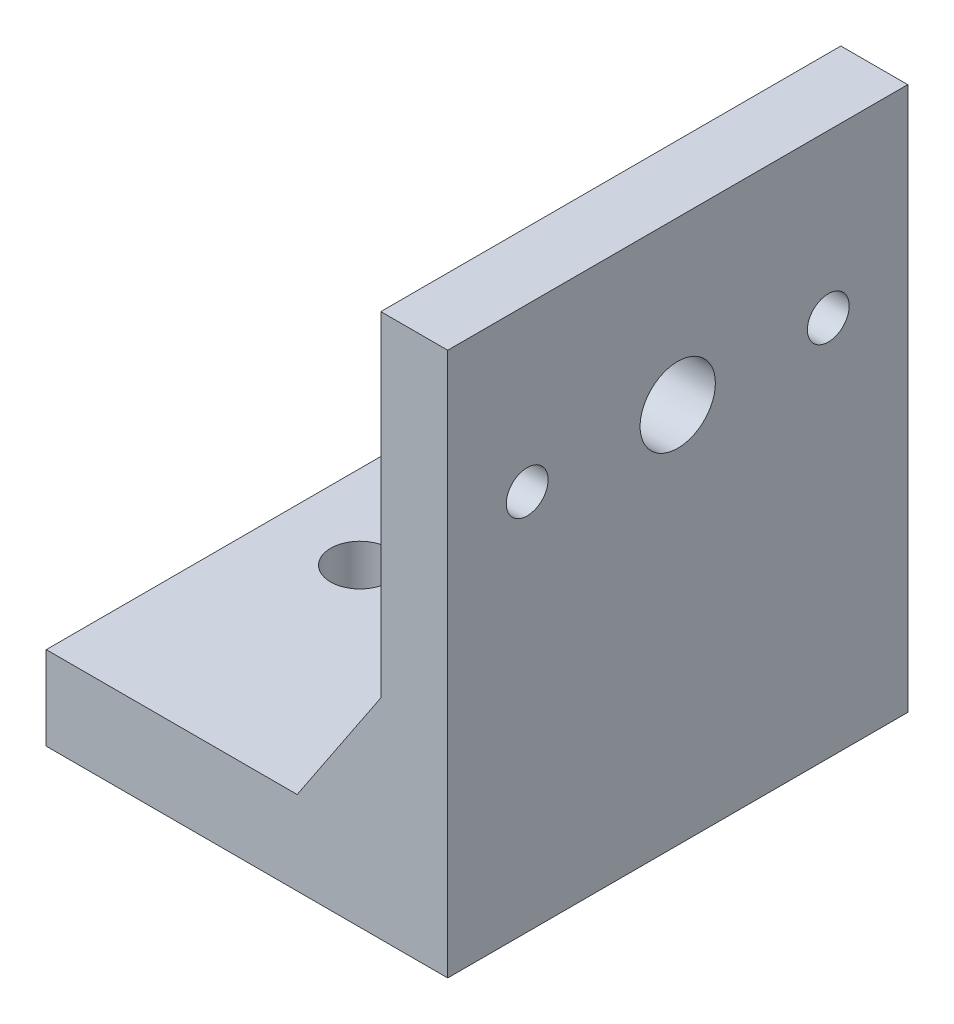
SolidWorks part; units mm, degrees
ref_plane "Front" through (0, 0, 0) normal (0, 0, 1) x (1, 0, 0)
ref_plane "Top" through (0, 0, 0) normal (0, 1, 0) x (1, 0, 0)
ref_plane "Right" through (0, 0, 0) normal (1, 0, 0) x (0, 0, -1)
sketch "Sketch1" plane through (0, 0, 0) normal (0, 1, 0) x (1, 0, 0)
  line L1 (-24, 27.5) -> (24, 27.5)
  line L2 (-24, 27.5) -> (-24, -27.5)
  line L3 (-24, -27.5) -> (24, -27.5)
  line L4 (24, 27.5) -> (24, -27.5)
  line L5 (-24, 27.5) -> (24, -27.5) construction
  line L6 (-24, -27.5) -> (24, 27.5) construction
  point P0 (0, 0)
  dimension "D1" = 48
  dimension "D2" = 55
extrude "Boss-Extrude1" add sketch "Sketch1" along normal blind 10
sketch "Sketch2" plane through (0, 0, 0) normal (0, 1, 0) x (1, 0, 0)
  line L0 (-24, -27.5) -> (24, -27.5) construction
  line L1 (24, 27.5) -> (16, 27.5)
  line L2 (24, 27.5) -> (24, -27.5)
  line L3 (24, -27.5) -> (16, -27.5)
  line L4 (16, 27.5) -> (16, -27.5)
  dimension "D1" = 8
extrude "Boss-Extrude2" add sketch "Sketch2" along normal blind 65
sketch "Sketch3" plane through (24, 0, 0) normal (1, 0, 0) x (0, 0, -1)
  line L0 (0, 50) -> (0, -50) construction
  line L1 (50, 0) -> (-50, 0) construction
  circle A0 centre (0, 45.6) radius 4.5
  dimension "D2" = 9
  dimension "D1" = 45.6
extrude "Cut-Extrude1" cut sketch "Sketch3" against normal blind 65
sketch "Sketch4" plane through (24, 0, 0) normal (1, 0, 0) x (0, 0, -1)
  line L0 (0, 45.6) -> (32.2223, 45.6) construction
  line L1 (32.2223, 45.6) -> (-21.539, 45.6) construction
  line L2 (0, 57.1732) -> (0, -38.5621) construction
  line L3 (0, 50) -> (0, -50) construction
  circle A0 centre (-18, 45.6) radius 2.5
  circle A1 centre (18, 45.6) radius 2.5
  dimension "D2" = 5
  dimension "D1" = 18
extrude "Cut-Extrude2" cut sketch "Sketch4" against normal blind 65
sketch "Sketch5" plane through (0, 0, 0) normal (0, 1, 0) x (1, 0, 0)
  line L0 (-53.2951, 0) -> (61.2951, 0) construction
  line L1 (-50, 0) -> (50, 0) construction
  line L2 (-24, 27.5) -> (-24, -27.5) construction
  line L3 (16, -27.5) -> (16, 27.5) construction
  circle A0 centre (-14, 0) radius 3.5
  circle A1 centre (4, 0) radius 3.5
  dimension "D1" = 7
  dimension "D2" = 7
  dimension "D3" = 10
  dimension "D4" = 12
extrude "Cut-Extrude4" cut sketch "Sketch5" along normal blind 65
sketch "Sketch8" plane through (0, 0, -27.5) normal (0, 0, -1) x (-1, 0, 0)
  line L0 (-16, 25) -> (-16, 10)
  line L1 (-16, 65) -> (-16, 10) construction
  line L4 (-16, 10) -> (-6, 10)
  line L5 (-16, 10) -> (24, 10) construction
  line L6 (-16, 25) -> (-6, 10)
  dimension "D1" = 15
  dimension "D2" = 10
extrude "Boss-Extrude3" add sketch "Sketch8" against normal blind 5
mirror "Mirror1" about plane through (0, 0, 0) normal (0, 0, 1) of "Boss-Extrude3"
